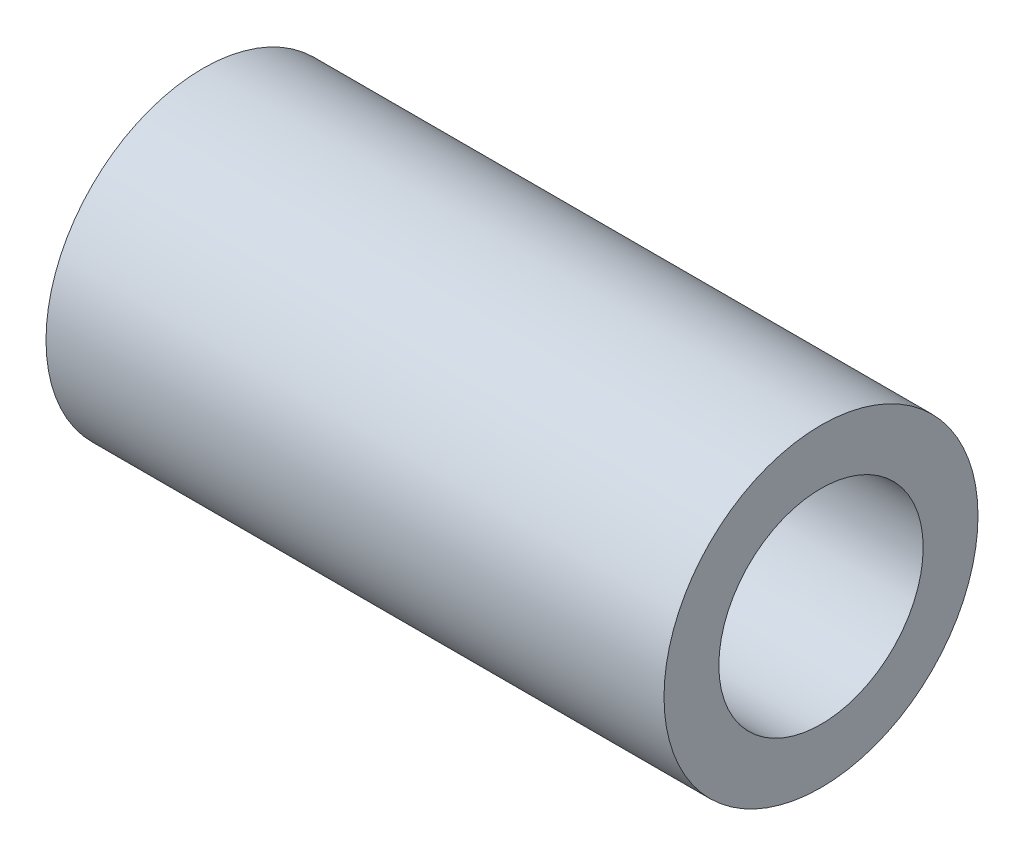
SolidWorks part; units mm, degrees
ref_plane "Alzado" through (0, 0, 0) normal (0, 0, 1) x (1, 0, 0)
ref_plane "Planta" through (0, 0, 0) normal (0, 1, 0) x (1, 0, 0)
ref_plane "Vista lateral" through (0, 0, 0) normal (1, 0, 0) x (0, 0, -1)
sketch "Croquis1" plane through (0, 0, 0) normal (0, 0, 1) x (1, 0, 0)
  line L0 (-12.4, 0) -> (12.4, 0) construction
  line L1 (-12.4, 6.3) -> (12.4, 6.3)
  line L2 (-12.4, 6.3) -> (-12.4, 4.1)
  line L3 (-12.4, 4.1) -> (12.4, 4.1)
  line L4 (12.4, 6.3) -> (12.4, 4.1)
  point P4 (0, 4.1)
  dimension "D1" = 6.3
  dimension "D2" = 4.1
  dimension "D3" = 24.8
revolve "Revolución1" add sketch "Croquis1" angle 360 about L0
